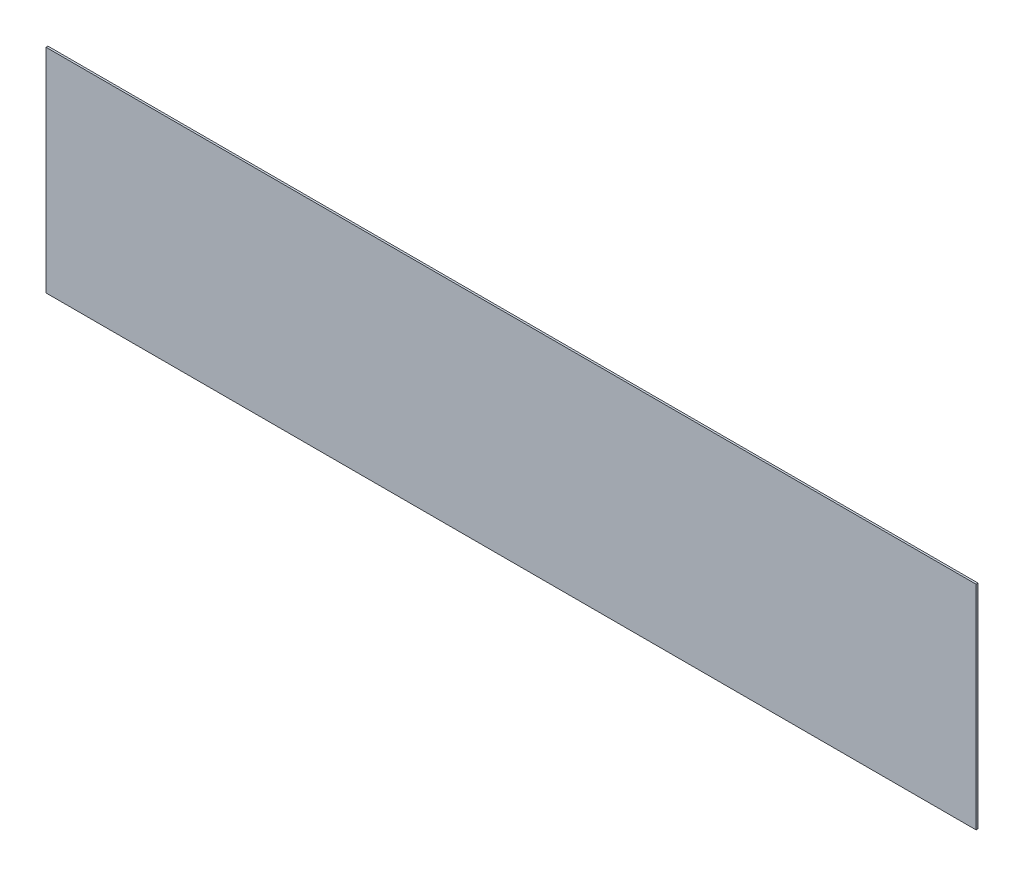
SolidWorks part; units mm, degrees
material "ABS PC"
ref_plane "Front Plane" through (0, 0, 0) normal (0, 0, 1) x (1, 0, 0)
ref_plane "Top Plane" through (0, 0, 0) normal (0, 1, 0) x (1, 0, 0)
ref_plane "Right Plane" through (0, 0, 0) normal (1, 0, 0) x (0, 0, -1)
sketch "Sketch1" plane through (0, 0, 0) normal (0, 0, 1) x (1, 0, 0)
  line L0 (-167.2098, -167.2126) -> (-167.2098, -188.0406) construction
  line L1 (-167.2098, -170.7686) -> (-107.2658, -170.7686)
  line L2 (-167.2098, -170.7686) -> (-167.2098, -184.4846)
  line L3 (-167.2098, -184.4846) -> (-107.2658, -184.4846)
  line L4 (-107.2658, -170.7686) -> (-107.2658, -184.4846)
  line L5 (-167.2098, -170.7686) -> (-107.2658, -184.4846) construction
  line L6 (-167.2098, -184.4846) -> (-107.2658, -170.7686) construction
  line L7 (-107.2658, -188.0406) -> (-107.2658, -167.2126) construction
  line L8 (-109.0438, -184.4846) -> (-165.4318, -184.4846) construction
  line L9 (-165.4318, -170.7686) -> (-109.0438, -170.7686) construction
  point P4 (-137.2378, -177.6266)
extrude "Boss-Extrude1" add sketch "Sketch1" along normal blind 0.127
